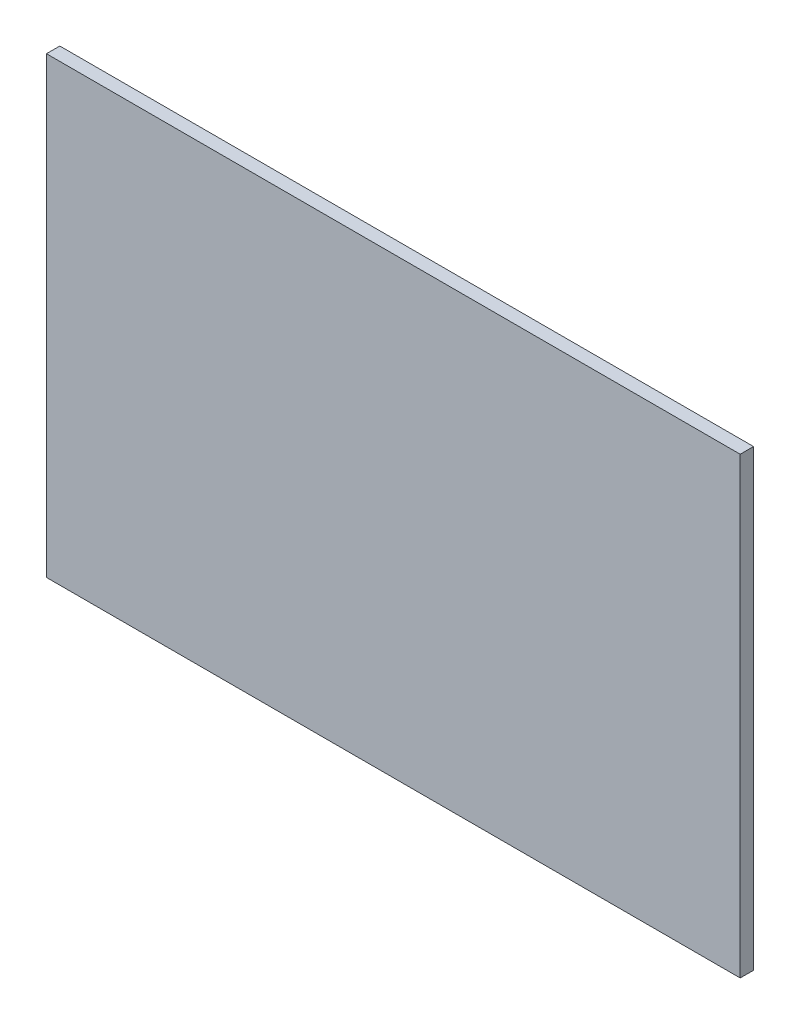
SolidWorks part; units mm, degrees
material "ALUMINUM 6061-T6"
ref_plane "Front Plane" through (0, 0, 0) normal (0, 0, 1) x (1, 0, 0)
ref_plane "Top Plane" through (0, 0, 0) normal (0, 1, 0) x (1, 0, 0)
ref_plane "Right Plane" through (0, 0, 0) normal (1, 0, 0) x (0, 0, -1)
sketch "Sketch1" plane through (0, 0, 0) normal (0, 0, 1) x (1, 0, 0)
  line L1 (-165.1, -107.95) -> (165.1, -107.95)
  line L2 (-165.1, -107.95) -> (-165.1, 107.95)
  line L3 (-165.1, 107.95) -> (165.1, 107.95)
  line L4 (165.1, -107.95) -> (165.1, 107.95)
  line L5 (-165.1, -107.95) -> (165.1, 107.95) construction
  line L6 (-165.1, 107.95) -> (165.1, -107.95) construction
  point P0 (0, 0)
  dimension "D1" = 330.2
  dimension "D2" = 215.9
extrude "Boss-Extrude1" add sketch "Sketch1" along normal mid plane 6.35
